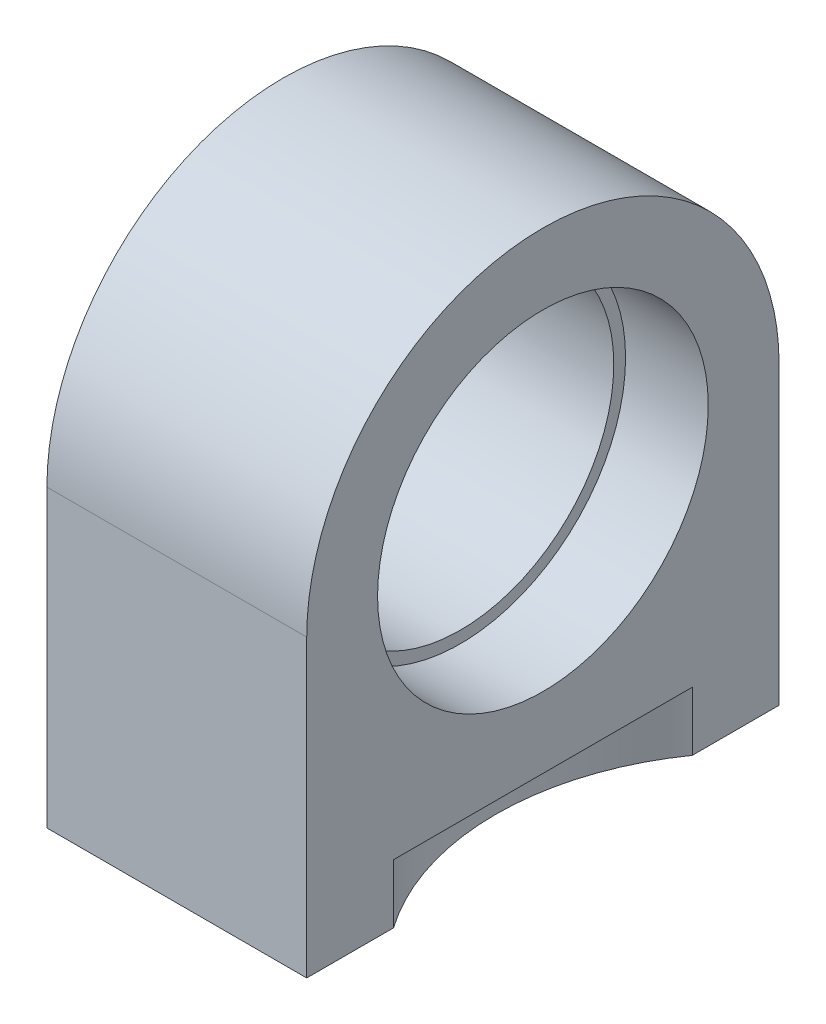
SolidWorks part; units mm, degrees
material "ABS"
ref_plane "Ebene vorne" through (0, 0, 0) normal (0, 0, 1) x (1, 0, 0)
ref_plane "Ebene oben" through (0, 0, 0) normal (0, 1, 0) x (1, 0, 0)
ref_plane "Ebene rechts" through (0, 0, 0) normal (1, 0, 0) x (0, 0, -1)
sketch "Skizze1" plane through (0, 0, 0) normal (1, 0, 0) x (0, 0, -1)
  line L0 (-10, 0) -> (-10, -12.5)
  line L1 (-10, -12.5) -> (10, -12.5)
  line L2 (10, -12.5) -> (10, 0)
  circle A0 centre (0, 0) radius 6.5
  arc A1 (-10, 0) -> (10, 0) centre (0, 0) cw
  dimension "D1" = 13
  dimension "D2" = 20
  dimension "D3" = 12.5
extrude "Aufsatz-Linear austragen1" add sketch "Skizze1" along normal blind 11
sketch "Skizze2" plane through (11, 0, 0) normal (1, 0, 0) x (0, 0, -1)
  circle A0 centre (0, 0) radius 7
  dimension "D1" = 14
extrude "Schnitt-Linear austragen1" cut sketch "Skizze2" against normal blind 3.5
sketch "Skizze3" plane through (0, -12.5, 0) normal (0, -1, 0) x (1, 0, 0)
  line L0 (0, 0) -> (10.0445, 0) construction
  line L2 (0, 10) -> (0, -10) construction
  circle A0 centre (6, 5) radius 2.75
  circle A1 centre (6, -5) radius 2.75
  dimension "D1" = 10
  dimension "D3" = 5.5
  dimension "D2" = 6
extrude "Schnitt-Linear austragen2" cut sketch "Skizze3" against normal blind 6
sketch "Skizze4" plane through (0, -12.5, 0) normal (0, -1, 0) x (1, 0, 0)
  circle A0 centre (20, 0) radius 11
  circle A1 centre (6, 5) radius 2.75 construction
  dimension "D1" = 14
  dimension "D2" = 22
extrude "Schnitt-Linear austragen3" cut sketch "Skizze4" against normal blind 2.5
